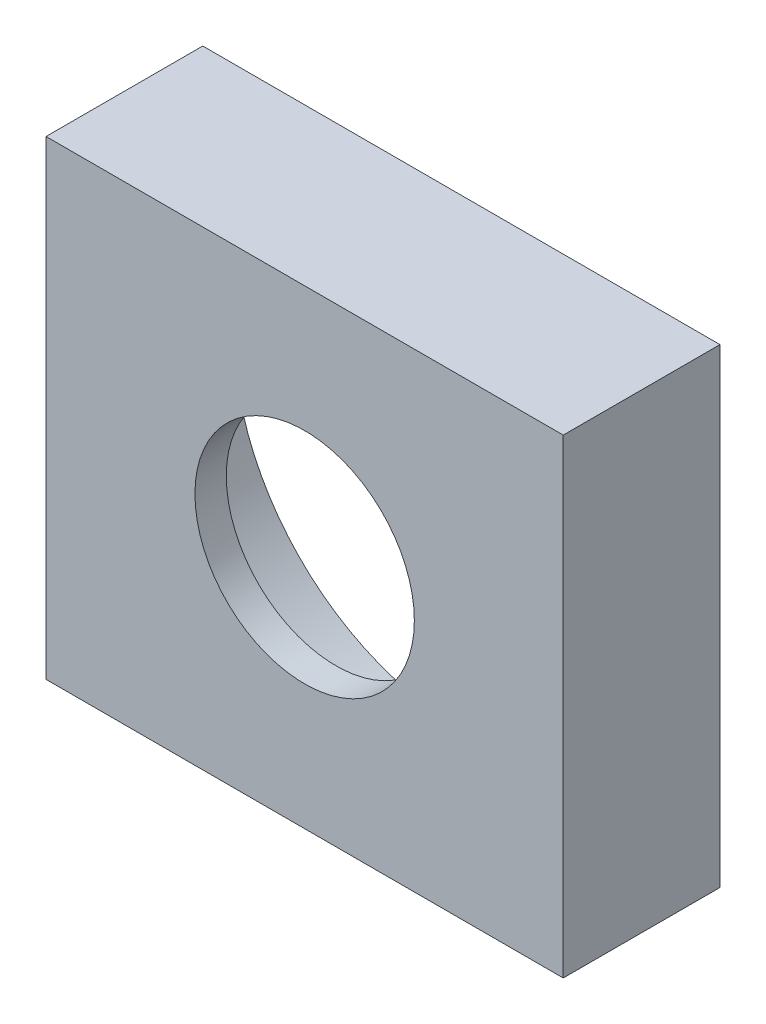
SolidWorks part; units mm, degrees
material "POM Acetal Copolymer"
ref_plane "Front Plane" through (0, 0, 0) normal (0, 0, 1) x (1, 0, 0)
ref_plane "Top Plane" through (0, 0, 0) normal (0, 1, 0) x (1, 0, 0)
ref_plane "Right Plane" through (0, 0, 0) normal (1, 0, 0) x (0, 0, -1)
sketch "Sketch1" plane through (0, 0, 0) normal (0, 0, 1) x (1, 0, 0)
  line L1 (0, 0) -> (33, 0)
  line L2 (0, 0) -> (0, 30)
  line L3 (0, 30) -> (33, 30)
  line L4 (33, 0) -> (33, 30)
  dimension "D1" = 30
  dimension "D2" = 33
extrude "Boss-Extrude1" add sketch "Sketch1" along normal blind 10
sketch "Sketch2" plane through (0, 0, 10) normal (0, 0, 1) x (1, 0, 0)
  line L0 (0, 30) -> (0, 0) construction
  line L1 (0, 0) -> (33, 0) construction
  circle A0 centre (16.5, 15) radius 7
  dimension "D1" = 14
  dimension "D2" = 16.5
  dimension "D3" = 15
extrude "Cut-Extrude1" cut sketch "Sketch2" against normal up to next
sketch "Sketch3" plane through (0, 0, 0) normal (0, 0, -1) x (-1, 0, 0)
  circle A0 centre (-16.5, 15) radius 14.5
  dimension "D1" = 29
extrude "Cut-Extrude2" cut sketch "Sketch3" against normal offset from surface (8 mm away) 2 up to face at (23.5, 15, 10)
hole_wizard "Tap Drill for M3 Tap2" positions "Sketch5" profile "Sketch4" hole size "M3" standard "ISO"
sketch "Sketch5" plane through (0, 0, 0) normal (0, -1, 0) x (-1, 0, 0)
  line L0 (0, -10) -> (-33, -10) construction
  line L1 (-33, -10) -> (-33, 0) construction
  line L2 (0, -10) -> (0, 0) construction
  point P0 (-3, -6)
  point P2 (-30, -6)
  dimension "D1" = 4
  dimension "D2" = 3
  dimension "D3" = 3
sketch "Sketch4" plane through (3, 0, 6) normal (1, 0, 0) x (0, 0, -1)
  line L0 (0, 0) -> (0, 8.7511)
  line L1 (0, 8.7511) -> (1.25, 8)
  line L2 (1.25, 8) -> (1.25, 0)
  line L5 (1.25, 0) -> (0, 0)
  line L10 (0, 8.7511) -> (-1.25, 8) construction
  line L11 (0, -6.35) -> (0, 107.95) construction
  dimension "Hole Dia." = 2.5
  dimension "Hole Depth" = 8
  dimension "Drill Angle" = 118
